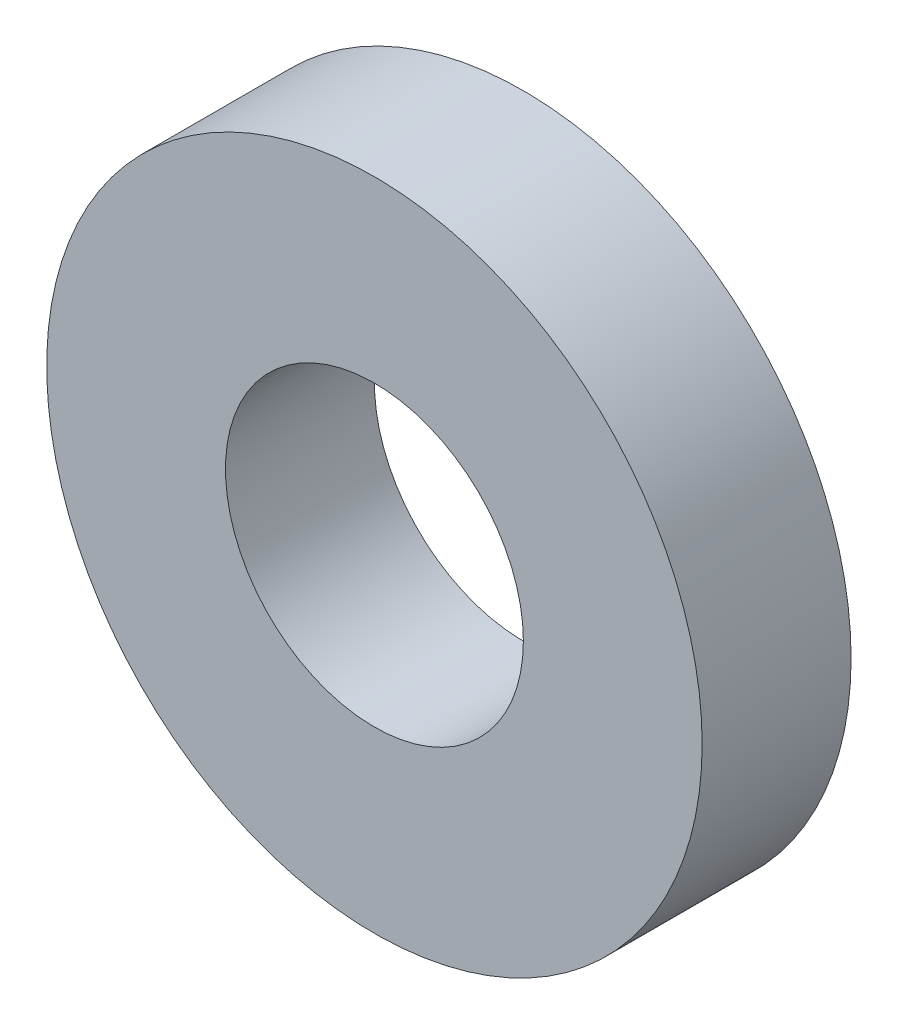
SolidWorks part; units mm, degrees
ref_plane "Front Plane" through (0, 0, 0) normal (0, 0, 1) x (1, 0, 0)
ref_plane "Top Plane" through (0, 0, 0) normal (0, 1, 0) x (1, 0, 0)
ref_plane "Right Plane" through (0, 0, 0) normal (1, 0, 0) x (0, 0, -1)
sketch "Sketch1" plane through (0, 0, 0) normal (0, 0, 1) x (1, 0, 0)
  circle A0 centre (0, 0) radius 6
  circle A1 centre (0, 0) radius 13.2
extrude "Boss-Extrude1" add sketch "Sketch1" along normal blind 6
sketch "Sketch2" plane through (0, 0, 6) normal (0, 0, 1) x (1, 0, 0)
  line L0 (0, 0) -> (0, 15.2) construction
  line L1 (-1.8199, 15.2) -> (0, 0) construction
  line L2 (1.8199, 15.2) -> (0, 0) construction
  arc A0 (-1.8199, 12) -> (1.8199, 12) centre (0, 0) cw
  arc A1 (-6.8199, 11.3018) -> (6.8199, 11.3018) centre (0, 0) cw
  arc A2 (-1.8199, 10.512) -> (1.8199, 10.512) centre (0, 0) cw
  arc A3 (-6.8199, 11.3018) -> (-1.8199, 12) centre (-4.3199, 11.6509) ccw
sketch "Sketch3" plane through (0, 0, 0) normal (0, 0, 1) x (1, 0, 0)
  circle A0 centre (0, 0) radius 6
  circle A1 centre (0, 0) radius 13.2
